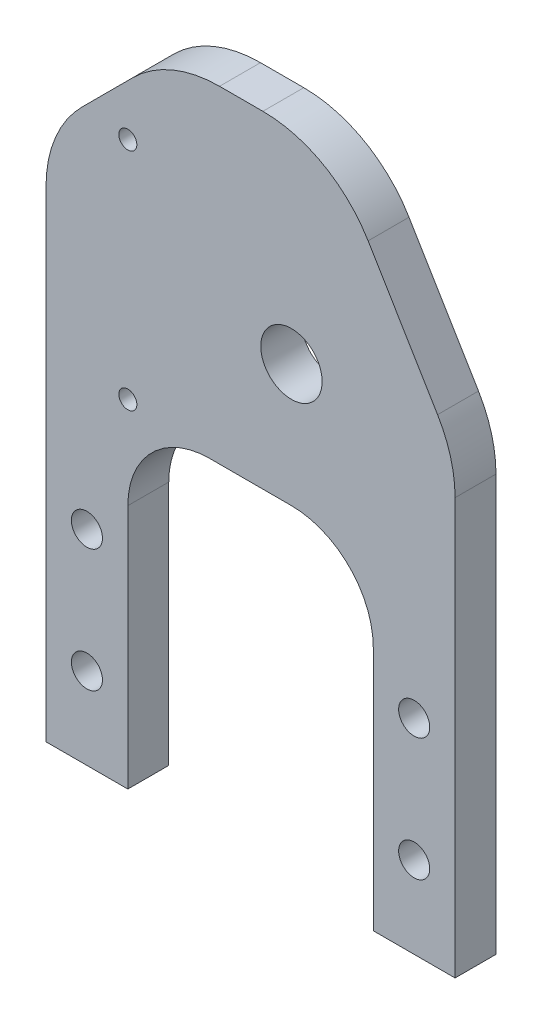
SolidWorks part; units mm, degrees
material "6061-T6 (SS)"
ref_plane "Front Plane" through (0, 0, 0) normal (0, 0, 1) x (1, 0, 0)
ref_plane "Top Plane" through (0, 0, 0) normal (0, 1, 0) x (1, 0, 0)
ref_plane "Right Plane" through (0, 0, 0) normal (1, 0, 0) x (0, 0, -1)
sketch "Sketch1" plane through (0, 0, 0) normal (0, 0, 1) x (1, 0, 0)
  line L1 (0, 0) -> (12.7, 0)
  line L2 (0, 0) -> (0, 82.55)
  line L5 (50.8, 0) -> (63.5, 0)
  line L8 (63.5, 0) -> (63.5, 69.85)
  line L13 (12.7, 0) -> (12.7, 50.8)
  line L14 (12.7, 50.8) -> (50.8, 50.8)
  line L15 (50.8, 50.8) -> (50.8, 0)
  line L17 (19.05, 101.6) -> (0, 82.55)
  line L18 (19.05, 101.6) -> (44.45, 101.6)
  line L19 (44.45, 101.6) -> (63.5, 69.85)
  dimension "D3" = 82.55
  dimension "D1" = 25.4
  dimension "D2" = 101.6
  dimension "D4" = 12.7
  dimension "D5" = 63.5
  dimension "D6" = 50.8
  dimension "D7" = 12.7
  dimension "D8" = 19.05
  dimension "D9" = 69.85
extrude "Boss-Extrude1" add sketch "Sketch1" along normal blind 6.35
sketch "Sketch2" plane through (0, 0, 6.35) normal (0, 0, 1) x (1, 0, 0)
  circle A0 centre (6.35, 12.7) radius 2.413
  circle A1 centre (6.35, 31.75) radius 2.413
  circle A2 centre (57.15, 12.7) radius 2.413
  circle A3 centre (57.15, 31.75) radius 2.413
  dimension "D1" = 4.826
  dimension "D2" = 4.826
  dimension "D3" = 6.35
  dimension "D4" = 12.7
  dimension "D5" = 19.05
  dimension "D6" = 50.8
extrude "Cut-Extrude1" cut sketch "Sketch2" against normal up to next
sketch "Sketch4" plane through (0, 0, 6.35) normal (0, 0, 1) x (1, 0, 0)
  line L0 (63.5, 0) -> (63.5, 69.85) construction
  line L1 (50.8, 0) -> (63.5, 0) construction
  circle A0 centre (12.7, 52.3875) radius 1.397
  circle A1 centre (12.7, 87.3125) radius 1.397
  circle A3 centre (38.1, 69.85) radius 4.7625
  point P4 (0, 0)
  point P5 (50.8, 54.2154)
  point P6 (66.8792, 68.8761)
  point P9 (52.6571, 70.2757)
  point P10 (50.8, 72.3958)
  point P11 (82.55, 69.85)
  point P14 (0, 0)
  point P17 (29.326, 87.2795)
  dimension "D1" = 2.794
  dimension "D7" = 9.525
  dimension "D2" = 34.925
  dimension "D3" = 25.4
  dimension "D4" = 69.85
  dimension "D5" = 17.4625
  dimension "D6" = 25.4
extrude "Cut-Extrude3" cut sketch "Sketch4" against normal up to next
fillet "Fillet4" radius 12.7 2 edges at (50.8, 50.8, 3.175) (12.7, 50.8, 3.175)
fillet "Fillet5" radius 19.05 4 edges at (0, 82.55, 3.175) (19.05, 101.6, 3.175) (44.45, 101.6, 3.175) (63.5, 69.85, 3.175)
